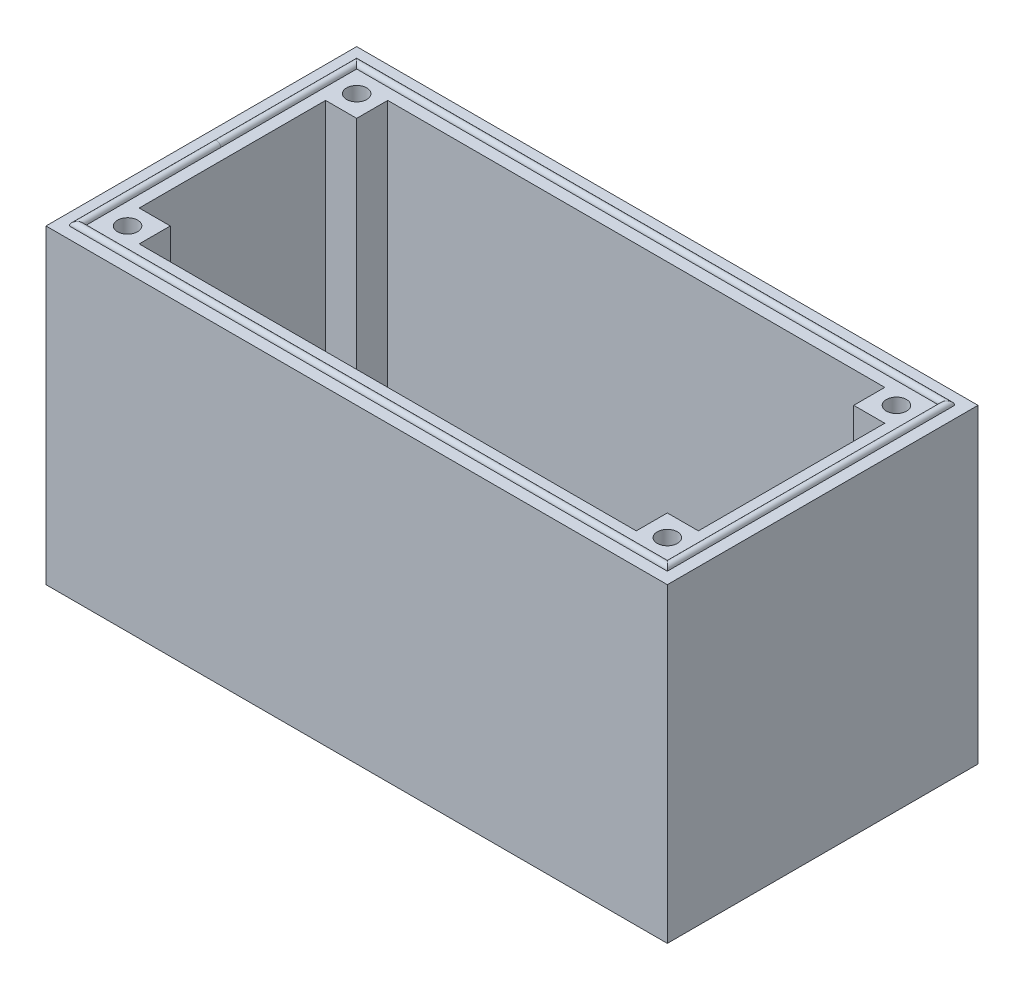
SolidWorks part; units mm, degrees
ref_plane "Piano frontale" through (0, 0, 0) normal (0, 0, 1) x (1, 0, 0)
ref_plane "Piano superiore" through (0, 0, 0) normal (0, 1, 0) x (1, 0, 0)
ref_plane "Piano destro" through (0, 0, 0) normal (1, 0, 0) x (0, 0, -1)
sketch "Schizzo1" plane through (0, 0, 0) normal (0, 0, 1) x (1, 0, 0)
  line L0 (0, 0) -> (0, 20)
  line L1 (0, 20) -> (40, 20)
  line L2 (40, 20) -> (40, 0)
  line L3 (40, 0) -> (0, 0)
  dimension "D1" = 40
  dimension "D2" = 20
extrude "Estrusione-Estrusione1" add sketch "Schizzo1" against normal blind 20
sketch "Schizzo2" plane through (0, 20, 0) normal (0, 1, 0) x (1, 0, 0)
  line L0 (0, 10) -> (40, 10) construction
  line L1 (0, 20) -> (0, 0) construction
  line L2 (40, 20) -> (40, 0) construction
  line L3 (20, 20) -> (20, 0) construction
  line L4 (40, 20) -> (0, 20) construction
  line L5 (40, 0) -> (0, 0) construction
  line L6 (4, 18) -> (4, 16)
  line L7 (36, 2) -> (4, 2)
  line L8 (38, 4) -> (38, 16)
  line L9 (36, 18) -> (4, 18)
  line L10 (2, 4) -> (2, 16)
  line L11 (36, 2.8889) -> (4, 17.1111) construction
  line L12 (36, 17.1111) -> (4, 2.8889) construction
  line L13 (4, 16) -> (2, 16)
  line L14 (2, 4) -> (4, 4)
  line L15 (4, 4) -> (4, 2)
  line L16 (36, 18) -> (36, 16)
  line L17 (36, 16) -> (38, 16)
  line L18 (38, 4) -> (36, 4)
  line L19 (36, 4) -> (36, 2)
  point P12 (20, 10)
  dimension "D1" = 2
  dimension "D2" = 2
  dimension "D3" = 2
extrude "Taglio-Estrusione1" cut sketch "Schizzo2" against normal blind 20 contours L8 L17 L16 L9 L6 L13 L10 L14 L15 L7 L19 L18
ref_plane "Piano1" through (0, 0, -10) normal (0, 0, 1) x (1, 0, 0)
sketch "Schizzo3" plane through (0, 0, -10) normal (0, 0, 1) x (1, 0, 0)
  line L0 (40, 20) -> (0, 20) construction
  line L1 (0.75, 20) -> (1.25, 20)
  arc A0 (1.25, 20) -> (0.75, 20) centre (1, 20) ccw
  point P0 (1.999, 20)
  dimension "D1" = 0.5
  dimension "D2" = 1
sketch "Schizzo4" plane through (0, 20, 0) normal (0, 1, 0) x (1, 0, 0)
  line L0 (0, 10) -> (40, 10) construction
  line L1 (0, 20) -> (0, 0) construction
  line L2 (-11.1375, 10) -> (11.1375, 10) construction
  line L3 (20, 0) -> (20, 20) construction
  line L4 (40, 0) -> (0, 0) construction
  line L5 (40, 20) -> (0, 20) construction
  line L6 (40, 20) -> (40, 0) construction
  line L7 (1, 19) -> (39, 19)
  line L8 (1, 19) -> (1, 1)
  line L9 (1, 1) -> (39, 1)
  line L10 (39, 19) -> (39, 1)
  line L11 (1, 19) -> (39, 1) construction
  line L12 (1, 1) -> (39, 19) construction
  point P12 (20, 10)
  dimension "D1" = 1
  dimension "D2" = 1
  dimension "D3" = 1
sweep "Sweep1" add profiles "Schizzo3" path "Schizzo4"
sketch "Schizzo5" plane through (0, 0, 0) normal (0, -1, 0) x (1, 0, 0)
  line L4 (1, -19) -> (39, -19)
  line L5 (1, -1) -> (1, -19)
  line L6 (39, -1) -> (1, -1)
  line L7 (39, -19) -> (39, -1)
  line L8 (1, -19) -> (39, -19)
  line L9 (1, -1) -> (1, -19)
  line L10 (39, -1) -> (1, -1)
  line L11 (39, -19) -> (39, -1)
  dimension "D1" = 0
sketch "Schizzo6" plane through (0, 0, -10) normal (0, 0, 1) x (1, 0, 0)
  line L0 (39, 0) -> (1, 0) construction
  line L1 (1, 0) -> (39, 0) construction
  line L2 (0, 20) -> (0, 0) construction
  line L3 (0.75, 0) -> (1.25, 0)
  arc A0 (1.25, 0) -> (0.75, 0) centre (1, 0) ccw
  dimension "D1" = 0.5
  dimension "D2" = 1
sweep "Taglia-Sweep1" cut profiles "Schizzo6" path "Schizzo5"
hole_wizard "Foro per Vite M1-1" positions "Schizzo7" profile "Schizzo9" hole size "M1" standard "KS" end condition through all
sketch "Schizzo7" plane through (0, 0, 0) normal (0, -1, 0) x (-1, 0, 0)
  line L4 (-38.75, 1.25) -> (-38.75, 18.75) construction
  line L5 (-38.75, 18.75) -> (-1.25, 18.75) construction
  point P0 (-37.375, 17.375)
  dimension "D1" = 1.375
  dimension "D2" = 1.375
sketch "Schizzo9" plane through (37.375, 0, -17.375) normal (1, 0, 0) x (0, 0, -1)
  line L0 (0, 0) -> (0, 20.25)
  line L1 (0, 20.25) -> (0.65, 20.25)
  line L2 (0.65, 20.25) -> (0.65, 0.025)
  line L3 (0.65, 0.025) -> (0.675, 0)
  line L5 (0.675, 0) -> (0, 0)
  line L6 (-0.65, 0.025) -> (-0.675, 0) construction
  line L11 (0, -6.35) -> (0, 107.95) construction
  dimension "Thru Hole Dia." = 1.3
  dimension "Thru Hole Depth" = 20.25
  dimension "Near C'Sink Dia." = 1.35
  dimension "Near C'Sink Angle" = 90
cosmetic thread "Cosmetic Thread5" parameters "D2"=2.3
mirror "Specchia1" about plane through (0, 0, -10) normal (0, 0, 1) of "Foro per Vite M1-1"
cosmetic thread "Cosmetic Thread6" parameters "D2"=2.3
ref_plane "Piano2" through (20, 0, 0) normal (1, 0, 0) x (0, 0, -1)
mirror "Specchia2" about plane through (20, 0, 0) normal (1, 0, 0) of "Specchia1", "Foro per Vite M1-1"
cosmetic thread "Cosmetic Thread7" parameters "D2"=2.3
cosmetic thread "Cosmetic Thread8" parameters "D2"=2.3
